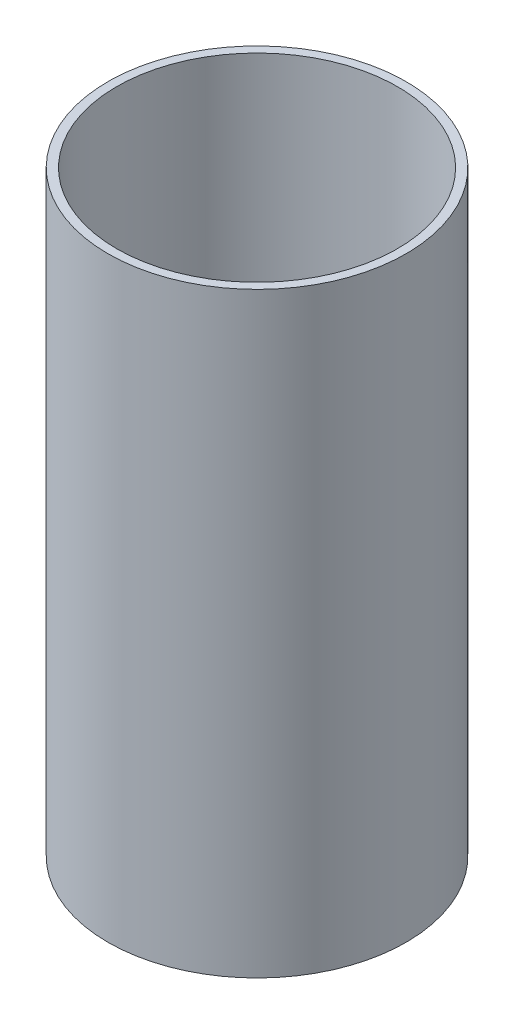
SolidWorks part; units mm, degrees
ref_plane "Front Plane" through (0, 0, 0) normal (0, 0, 1) x (1, 0, 0)
ref_plane "Top Plane" through (0, 0, 0) normal (0, 1, 0) x (1, 0, 0)
ref_plane "Right Plane" through (0, 0, 0) normal (1, 0, 0) x (0, 0, -1)
sketch "Sketch1" plane through (0, 0, 0) normal (0, 1, 0) x (1, 0, 0)
  circle A0 centre (0, 0) radius 6.35
  circle A1 centre (0, 0) radius 5.9808
  dimension "D1" = 12.7
  dimension "D2" = 11.9615
sketch "Sketch2" plane through (0, 0, 0) normal (1, 0, 0) x (0, 0, -1)
  line L0 (0, 0) -> (0, -25.4)
  dimension "D1" = 25.4
sweep "Sweep1" add profiles "Sketch1" path "Sketch2"
